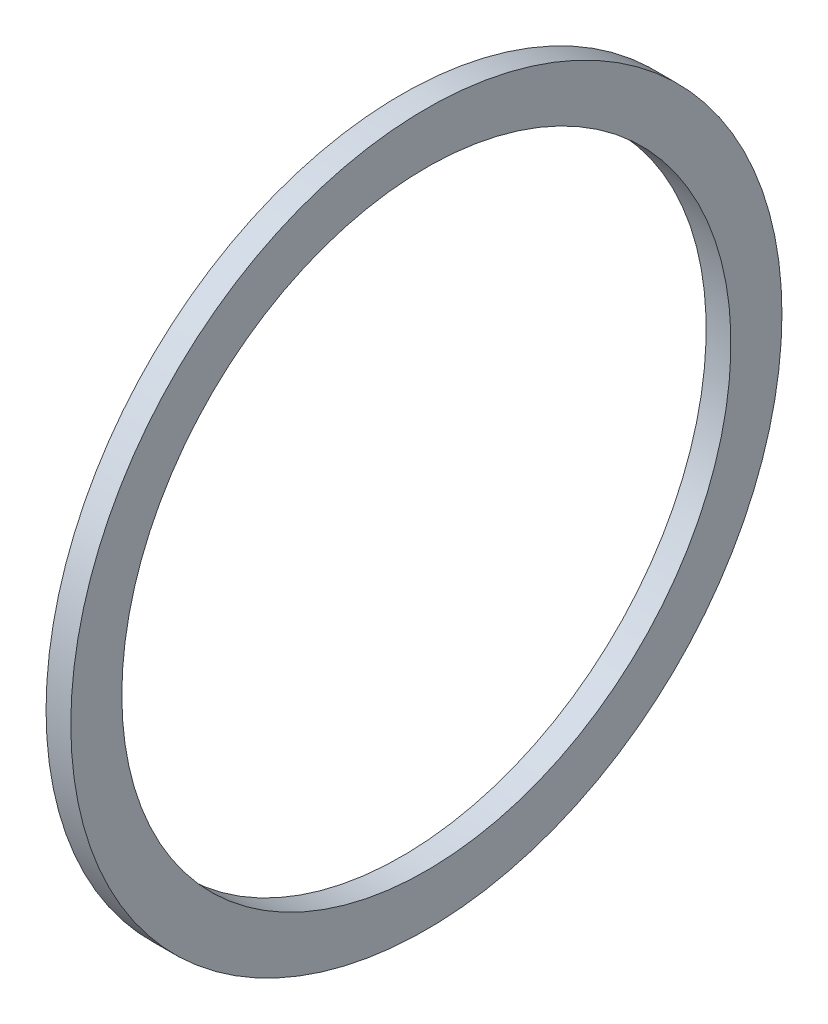
SolidWorks part; units mm, degrees
ref_plane "Front Plane" through (0, 0, 0) normal (0, 0, 1) x (1, 0, 0)
ref_plane "Top Plane" through (0, 0, 0) normal (0, 1, 0) x (1, 0, 0)
ref_plane "Right Plane" through (0, 0, 0) normal (1, 0, 0) x (0, 0, -1)
sketch "Sketch1" plane through (0, 0, 0) normal (0, 0, 1) x (1, 0, 0)
  line L0 (-43.7166, 0) -> (79.6876, 0) construction
  line L2 (0, -25.019) -> (2.032, -25.019)
  line L3 (0, -25.019) -> (0, -29.21)
  line L4 (0, -29.21) -> (2.032, -29.21)
  line L5 (2.032, -25.019) -> (2.032, -29.21)
  dimension "A" = 50.038
  dimension "B" = 58.42
  dimension "C" = 2.032
revolve "Revolve1" add sketch "Sketch1" angle 360 about L0
sketch "Sketch2" [suppressed] plane through (0, 0, 0) normal (0, 0, 1) x (1, 0, 0)
  line L0 (-34.685, 0) -> (47.6686, 0) construction
  circle A0 centre (2.54, -5.715) radius 0.762
  dimension "D1" = 2.54
  dimension "E" = 2.032
  dimension "D" = 42.926
revolve "Revolve3" [suppressed] add sketch "Sketch2" angle 360 about L0
